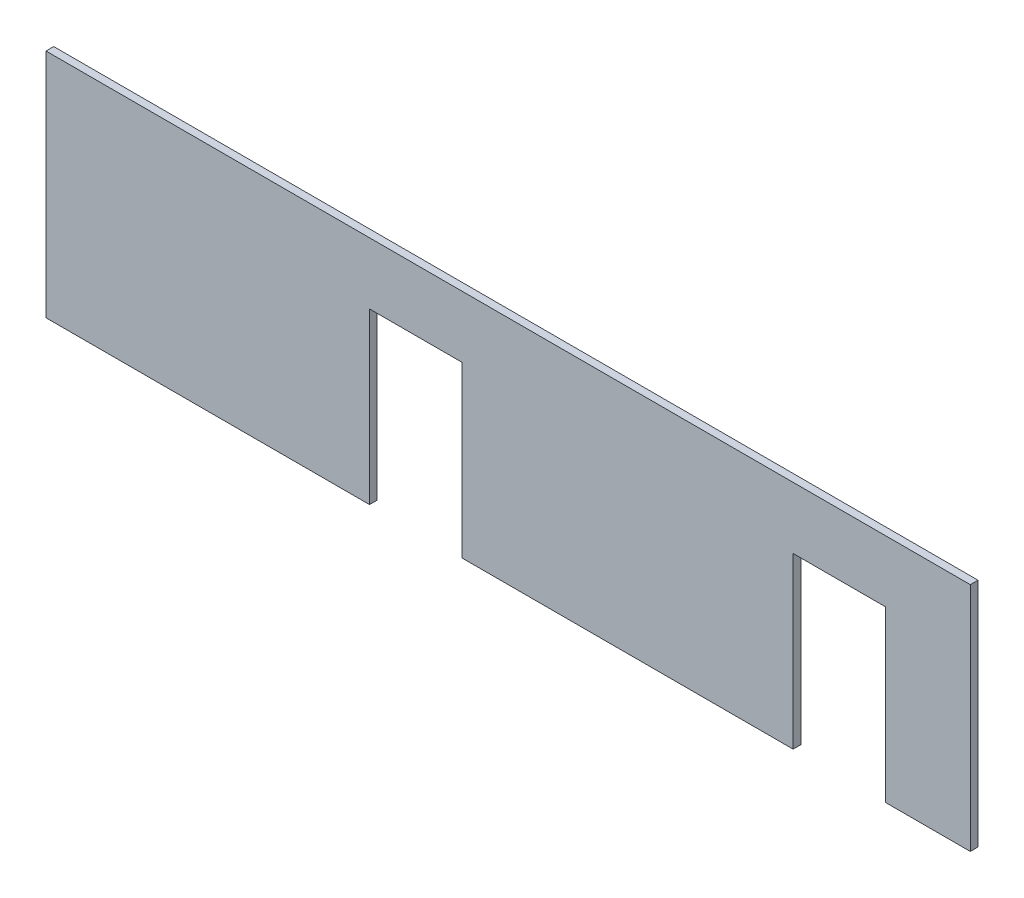
SolidWorks part; units mm, degrees
ref_plane "Front Plane" through (0, 0, 0) normal (0, 0, 1) x (1, 0, 0)
ref_plane "Top Plane" through (0, 0, 0) normal (0, 1, 0) x (1, 0, 0)
ref_plane "Right Plane" through (0, 0, 0) normal (1, 0, 0) x (0, 0, -1)
sketch "Sketch1" plane through (0, 0, 0) normal (0, 0, 1) x (1, 0, 0)
  line L0 (-130, 75) -> (-130, -75) construction
  line L1 (-300, 75) -> (300, 75)
  line L2 (-300, 75) -> (-300, -75)
  line L3 (-300, -75) -> (-90, -75)
  line L4 (300, 75) -> (300, -75)
  line L5 (-300, 75) -> (300, -75) construction
  line L6 (-300, -75) -> (300, 75) construction
  line L11 (245, -75) -> (245, 35)
  line L20 (130, 75) -> (130, -75) construction
  line L21 (-30, -75) -> (-30, 35)
  line L22 (185, 35) -> (185, -75)
  line L23 (185, 35) -> (245, 35)
  line L24 (245, -75) -> (300, -75)
  line L25 (-30, 35) -> (-90, 35)
  line L26 (-90, 35) -> (-90, -75)
  line L27 (-30, -75) -> (185, -75)
  point P0 (0, 0)
  point P15 (0, 0)
  point P16 (-60, 35)
  point P18 (215, 35)
  dimension "D1" = 600
  dimension "D2" = 150
  dimension "D3" = 170
  dimension "D4" = 170
  dimension "D5" = 110
  dimension "D6" = 60
  dimension "D7" = 70
  dimension "D8" = 60
  dimension "D9" = 85
  dimension "D10" = 110
extrude "Boss-Extrude1" add sketch "Sketch1" along normal blind 5
